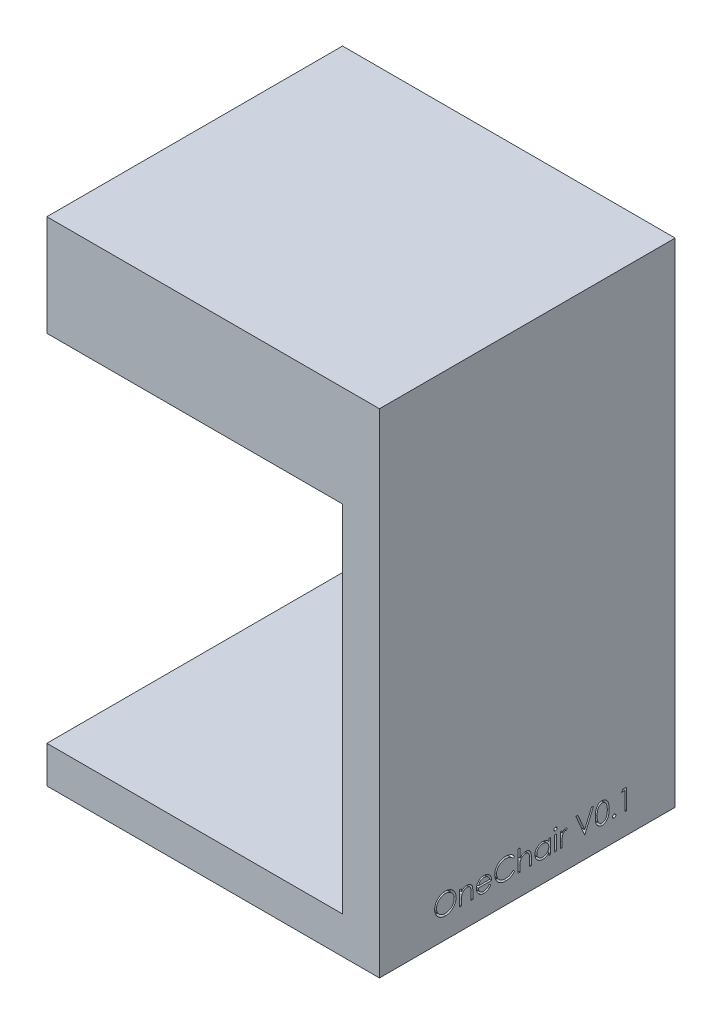
SolidWorks part; units mm, degrees
ref_plane "Front Plane" through (0, 0, 0) normal (0, 0, 1) x (1, 0, 0)
ref_plane "Top Plane" through (0, 0, 0) normal (0, 1, 0) x (1, 0, 0)
ref_plane "Right Plane" through (0, 0, 0) normal (1, 0, 0) x (0, 0, -1)
sketch "Sketch1" plane through (0, 0, 0) normal (0, 1, 0) x (1, 0, 0)
  line L1 (-25.4, -25.4) -> (25.4, -25.4)
  line L2 (-25.4, -25.4) -> (-25.4, 25.4)
  line L3 (-25.4, 25.4) -> (25.4, 25.4)
  line L4 (25.4, -25.4) -> (25.4, 25.4)
  line L5 (-25.4, -25.4) -> (25.4, 25.4) construction
  line L6 (-25.4, 25.4) -> (25.4, -25.4) construction
  point P0 (0, 0)
  dimension "D1" = 50.8
  dimension "D2" = 50.8
extrude "Boss-Extrude1" add sketch "Sketch1" along normal blind 6.35
sketch "Sketch2" plane through (0, 0, 0) normal (0, 1, 0) x (1, 0, 0)
  line L1 (25.4, -25.4) -> (31.75, -25.4)
  line L2 (25.4, -25.4) -> (25.4, 25.4)
  line L3 (25.4, 25.4) -> (31.75, 25.4)
  line L4 (31.75, -25.4) -> (31.75, 25.4)
  dimension "D1" = 6.35
extrude "Boss-Extrude3" add sketch "Sketch2" along normal blind 6.35
sketch "Sketch3" plane through (0, 6.35, 0) normal (0, 1, 0) x (1, 0, 0)
  line L0 (-25.4, -25.4) -> (31.75, -25.4) construction
  line L1 (31.75, 25.4) -> (25.4, 25.4)
  line L2 (31.75, 25.4) -> (31.75, -25.4)
  line L3 (31.75, -25.4) -> (25.4, -25.4)
  line L4 (25.4, 25.4) -> (25.4, -25.4)
  line L5 (-25.4, 25.4) -> (-25.4, -25.4) construction
  dimension "D1" = 50.8
extrude "Boss-Extrude4" add sketch "Sketch3" along normal blind 61 contours L2 L1 L4 L3
sketch "Sketch4" plane through (0, 67.35, 0) normal (0, 1, 0) x (1, 0, 0)
  line L1 (31.75, 25.4) -> (-25.4, 25.4)
  line L2 (31.75, 25.4) -> (31.75, -25.4)
  line L3 (31.75, -25.4) -> (-25.4, -25.4)
  line L4 (-25.4, 25.4) -> (-25.4, -25.4)
extrude "Boss-Extrude5" add sketch "Sketch4" along normal blind 11
sketch "Sketch7" plane through (0, 78.35, 0) normal (0, 1, 0) x (1, 0, 0)
  line L4 (-25.4, -25.4) -> (31.75, -25.4)
  line L5 (-25.4, -25.4) -> (-25.4, 25.4)
  line L6 (-25.4, 25.4) -> (31.75, 25.4)
  line L7 (31.75, -25.4) -> (31.75, 25.4)
  line L8 (-25.4, -25.4) -> (31.75, 25.4) construction
  line L9 (-25.4, 25.4) -> (31.75, -25.4) construction
  point P6 (3.175, 0)
extrude "Boss-Extrude7" add sketch "Sketch7" along normal blind 6.35
sketch "Sketch9" plane through (-25.4, 0, 0) normal (-1, 0, 0) x (0, 0, 1)
  line L0 (-25.4, 84.7) -> (25.4, 84.7) construction
  circle A0 centre (0, 84.7) radius 11
sketch "Sketch11" plane through (31.75, 0, 0) normal (1, 0, 0) x (0, 0, -1)
  text T0 "OneChair V0.1"
extrude "Cut-Extrude3" cut sketch "Sketch11" against normal blind 1
